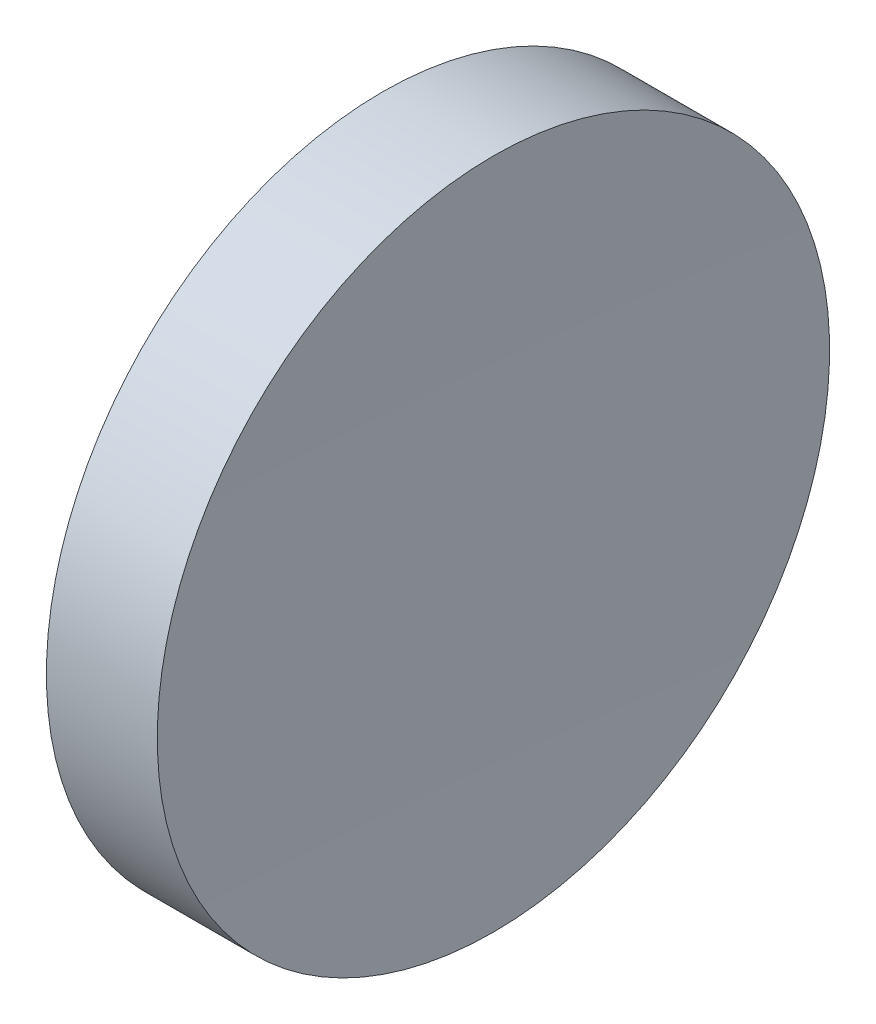
SolidWorks part; units mm, degrees
ref_plane "前视基准面" through (0, 0, 0) normal (0, 0, 1) x (1, 0, 0)
ref_plane "上视基准面" through (0, 0, 0) normal (0, 1, 0) x (1, 0, 0)
ref_plane "右视基准面" through (0, 0, 0) normal (1, 0, 0) x (0, 0, -1)
sketch "草图1" plane through (0, 0, 0) normal (0, 0, 1) x (1, 0, 0)
  line L0 (57.9722, 32.6084) -> (67.9741, 32.6084) construction
  line L1 (61.4936, 38.8584) -> (63.5553, 38.8584)
  line L2 (61.2739, 32.6084) -> (63.4739, 32.6084)
  arc A0 (61.4936, 38.8584) -> (61.2739, 32.6084) centre (150.2739, 32.6084) ccw
  arc A1 (63.5553, 38.8584) -> (63.4739, 32.6084) centre (303.4739, 32.6084) ccw
revolve "旋转1" add sketch "草图1" angle 360 about L0
